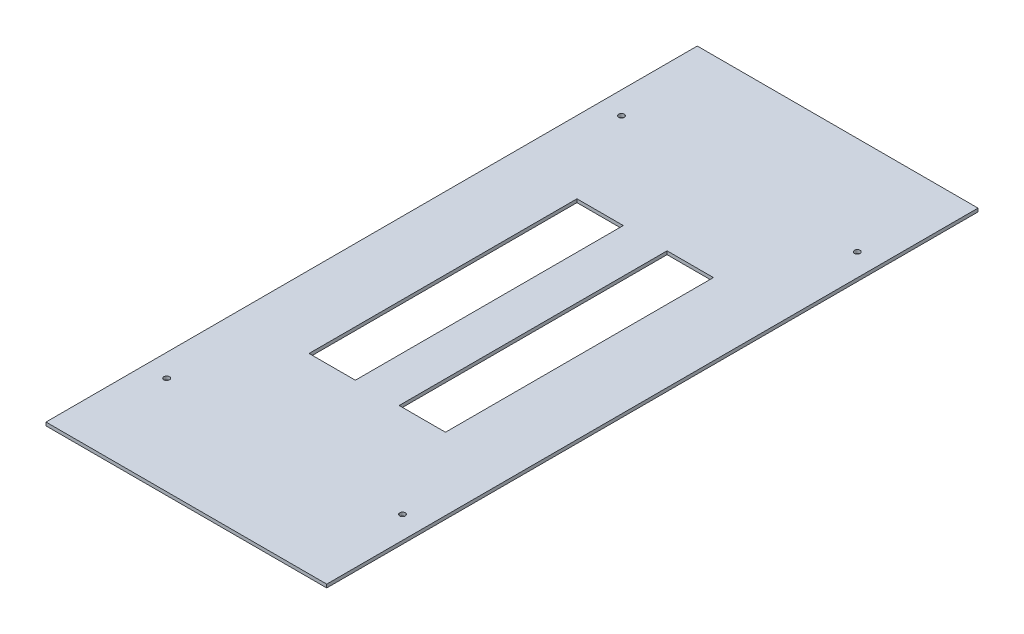
SolidWorks part; units mm, degrees
material "Acrylic (Medium-high impact)"
ref_plane "Front Plane" through (0, 0, 0) normal (0, 0, 1) x (1, 0, 0)
ref_plane "Top Plane" through (0, 0, 0) normal (0, 1, 0) x (1, 0, 0)
ref_plane "Right Plane" through (0, 0, 0) normal (1, 0, 0) x (0, 0, -1)
sketch "Sketch1" plane through (0, 0, 0) normal (0, 1, 0) x (1, 0, 0)
  line L0 (0, 212.5) -> (0, -212.5) construction
  line L1 (-115, 212.5) -> (115, 212.5)
  line L2 (-115, 212.5) -> (-115, -212.5)
  line L3 (-115, -212.5) -> (115, -212.5)
  line L4 (115, 212.5) -> (115, -212.5)
  line L5 (-115, 212.5) -> (115, -212.5) construction
  line L6 (-115, -212.5) -> (115, 212.5) construction
  line L8 (-115, 0) -> (115, 0) construction
  point P0 (0, 0)
  point P8 (-105, 202.5)
  point P14 (105, 202.5)
  point P16 (105, -202.5)
  point P17 (-105, -202.5)
  dimension "D1" = 210
  dimension "D2" = 405
  dimension "D3" = 10
  dimension "D4" = 10
extrude "Boss-Extrude1" add sketch "Sketch1" against normal blind 3 contours L1 L4 L3 L2
hole_wizard "Ø5.0 (4) Diameter Hole1" positions "Sketch2" profile "Sketch4" hole size "Ø5.0" standard "ANSI Metric" end condition through all
sketch "Sketch2" plane through (0, 0, 0) normal (0, 1, 0) x (1, 0, 0)
  point P0 (-105, 202.5)
  point P3 (105, 202.5)
  point P6 (105, -202.5)
  point P9 (-105, -202.5)
sketch "Sketch4" plane through (-105, 0, -202.5) normal (1, 0, 0) x (0, 0, 1)
  line L0 (0, 0) -> (0, 3)
  line L1 (0, 3) -> (2.5, 3)
  line L2 (2.5, 3) -> (2.5, 0)
  line L5 (2.5, 0) -> (0, 0)
  line L11 (0, -6.35) -> (0, 107.95) construction
  dimension "Thru Hole Dia." = 5
  dimension "Thru Hole Depth" = 3
sketch "Sketch5" plane through (0, 0, 0) normal (0, 1, 0) x (1, 0, 0)
  line L0 (0, 212.5) -> (0, -212.5) construction
  line L1 (-55.75, 113.6) -> (-24.5, 113.6) construction
  line L2 (-55.75, 113.6) -> (-55.75, -115) construction
  line L3 (-55.75, -115) -> (-24.5, -115) construction
  line L4 (-24.5, 113.6) -> (-24.5, -115) construction
  line L5 (24.5, 113.6) -> (24.5, -115) construction
  line L6 (-60.75, 118.6) -> (-19.5, 118.6)
  line L7 (-60.75, 118.6) -> (-60.75, -120)
  line L8 (-60.75, -120) -> (-19.5, -120)
  line L9 (-19.5, 118.6) -> (-19.5, -120)
  line L10 (55.75, -115) -> (24.5, -115) construction
  line L11 (55.75, 113.6) -> (55.75, -115) construction
  line L12 (55.75, 113.6) -> (24.5, 113.6) construction
  line L13 (19.5, 118.6) -> (19.5, -120)
  line L14 (60.75, -120) -> (19.5, -120)
  line L15 (60.75, 118.6) -> (60.75, -120)
  line L16 (60.75, 118.6) -> (19.5, 118.6)
  dimension "D1" = 88.9
  dimension "D2" = 228.6
  dimension "D3" = 55.75
  dimension "D4" = 5
  dimension "D5" = 5
  dimension "D6" = 5
  dimension "D7" = 5
  dimension "D8" = 24.5
extrude "Cut-Extrude1" cut sketch "Sketch5" against normal through all
sketch "Sketch6" plane through (0, 0, 0) normal (0, 1, 0) x (1, 0, 0)
  line L1 (-115, -212.5) -> (115, -212.5)
  line L2 (-115, -212.5) -> (-115, 212.5)
  line L3 (-115, 212.5) -> (115, 212.5)
  line L4 (115, -212.5) -> (115, 212.5)
  line L5 (-115, -212.5) -> (115, 212.5) construction
  line L6 (-115, 212.5) -> (115, -212.5) construction
  line L7 (-125, -290) -> (125, -290)
  line L8 (-125, -290) -> (-125, 290)
  line L9 (-125, 290) -> (125, 290)
  line L10 (125, -290) -> (125, 290)
  line L11 (-125, -290) -> (125, 290) construction
  line L12 (-125, 290) -> (125, -290) construction
  point P0 (0, 0)
  point P7 (0, 0)
  dimension "D1" = 250
  dimension "D2" = 580
extrude "Boss-Extrude3" add sketch "Sketch6" against normal up to surface (3 mm away) up to face at (-40.125, -3, 0.7)
